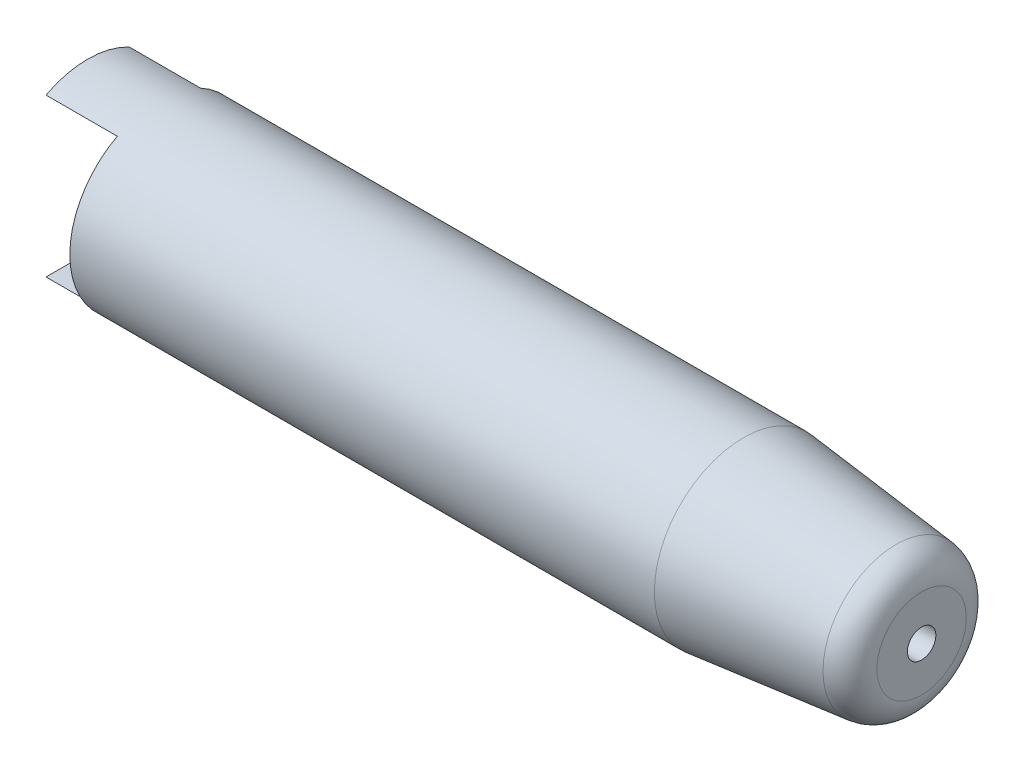
SolidWorks part; units mm, degrees
ref_plane "Plan de face" through (0, 0, 0) normal (0, 0, 1) x (1, 0, 0)
ref_plane "Plan de dessus" through (0, 0, 0) normal (0, 1, 0) x (1, 0, 0)
ref_plane "Plan de droite" through (0, 0, 0) normal (1, 0, 0) x (0, 0, -1)
sketch "Esquisse1" plane through (0, 0, 0) normal (0, 0, 1) x (1, 0, 0)
  line L0 (0, 0) -> (102.4289, 0) construction
  line L1 (56.6188, 2) -> (52, 10)
  line L4 (0, 12.5) -> (92, 12.5)
  line L5 (92, 12.5) -> (113.4181, 10.2489)
  line L6 (117, 6.2708) -> (117, 2)
  line L10 (0, 10) -> (52, 10)
  line L11 (0, 12.5) -> (0, 10)
  line L12 (56.6188, 2) -> (117, 2)
  arc A0 (113.4181, 10.2489) -> (117, 6.2708) centre (113, 6.2708) cw
  point P5 (0, 7.9769)
  point P13 (0.124, 7.9769)
  dimension "D7" = 4
  dimension "D1" = 117
  dimension "D2" = 2
  dimension "D3" = 25
  dimension "D4" = 6
  dimension "D5" = 12.5
  dimension "D6" = 10
  dimension "D8" = 60
  dimension "D9" = 52
revolve "Révolution1" add sketch "Esquisse1" angle 360 about L0
sketch "Esquisse2" plane through (0, 0, 0) normal (0, 0, 1) x (1, 0, 0)
  line L0 (0, -11.05) -> (0, 11.05)
  line L2 (0, 11.05) -> (10, 11.05)
  line L3 (10, 11.05) -> (10, -11.05)
  line L4 (10, -11.05) -> (0, -11.05)
  point P0 (5, -11.05)
  point P4 (0, 0)
  dimension "D1" = 10
  dimension "D2" = 22.1
extrude "Enlèv. mat.-Extru.1" cut sketch "Esquisse2" against normal mid plane 30 contours L0 L2 L3 L4
